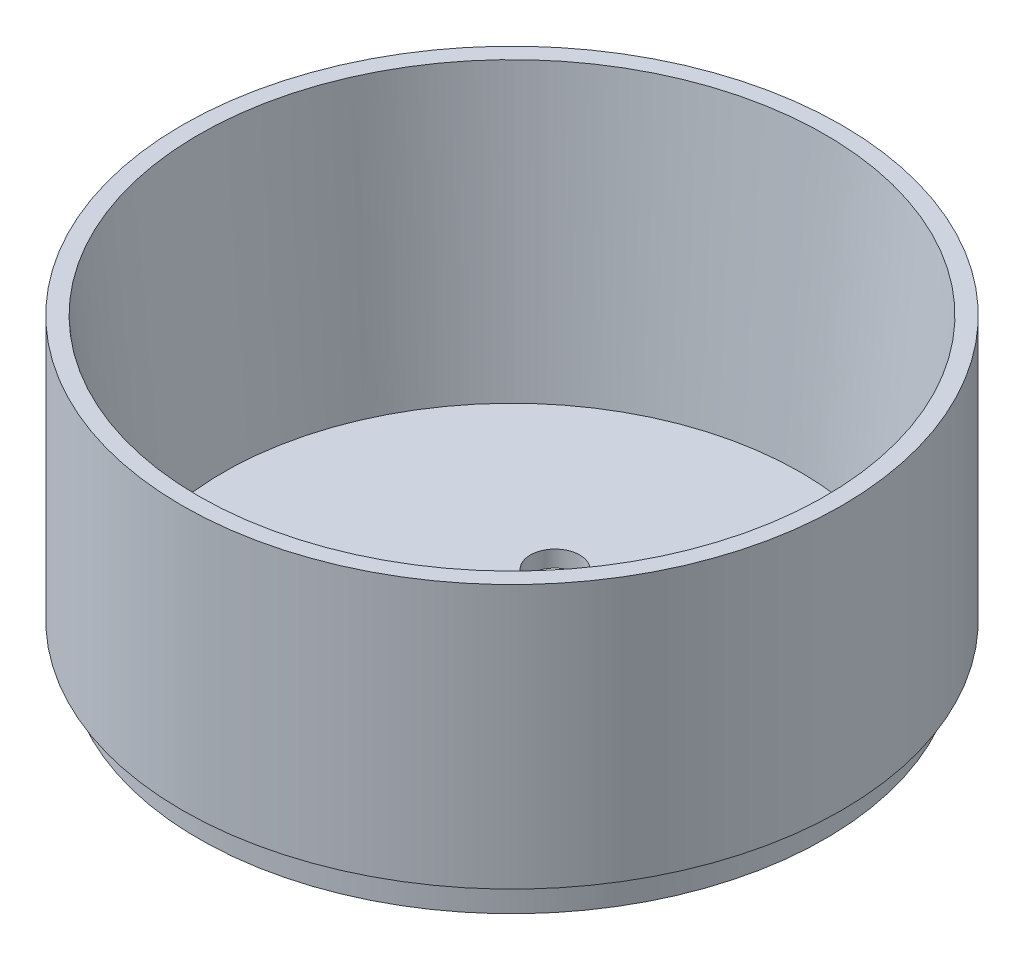
SolidWorks part; units mm, degrees
ref_plane "Front Plane" through (0, 0, 0) normal (0, 0, 1) x (1, 0, 0)
ref_plane "Top Plane" through (0, 0, 0) normal (0, 1, 0) x (1, 0, 0)
ref_plane "Right Plane" through (0, 0, 0) normal (1, 0, 0) x (0, 0, -1)
sketch "Sketch1" plane through (0, 0, 0) normal (0, 1, 0) x (1, 0, 0)
  circle A0 centre (0, 0) radius 63.5
  dimension "D1" = 127
extrude "Boss-Extrude1" add sketch "Sketch1" along normal blind 50.8
sketch "Sketch2" plane through (0, 0, 0) normal (0, -1, 0) x (1, 0, 0)
  circle A0 centre (0, 0) radius 60.325
  circle A1 centre (0, 0) radius 57.15
  dimension "D1" = 120.65
  dimension "D2" = 114.3
extrude "Boss-Extrude2" add sketch "Sketch2" along normal blind 6.35 contours A1 | A0 A1
sketch "Sketch3" plane through (0, 50.8, 0) normal (0, 1, 0) x (1, 0, 0)
  circle A0 centre (0, 0) radius 60.325
  dimension "D1" = 120.65
extrude "Cut-Extrude1" cut sketch "Sketch3" against normal offset from surface 3.175 draft 5 contours A0
sketch "Sketch4" plane through (0, -3.175, 0) normal (0, 1, 0) x (1, 0, 0)
  circle A0 centre (7.4871, -15.776) radius 4.7625 construction
  circle A1 centre (0, 0) radius 55.6028
  circle A2 centre (0, 0) radius 55.6028
  circle A3 centre (-7.4871, 15.776) radius 4.7625 construction
  circle A4 centre (0, 0) radius 4.7625 construction
  circle A5 centre (7.4871, -15.776) radius 4.7625
  circle A6 centre (-7.4871, 15.776) radius 4.7625
  circle A7 centre (0, 0) radius 4.7625
  dimension "D1" = 0
extrude "Cut-Extrude3" cut sketch "Sketch4" against normal up to surface (3.175 mm away) contours A5 | A7 | A6 up to face at (0, -6.35, -60.325)
